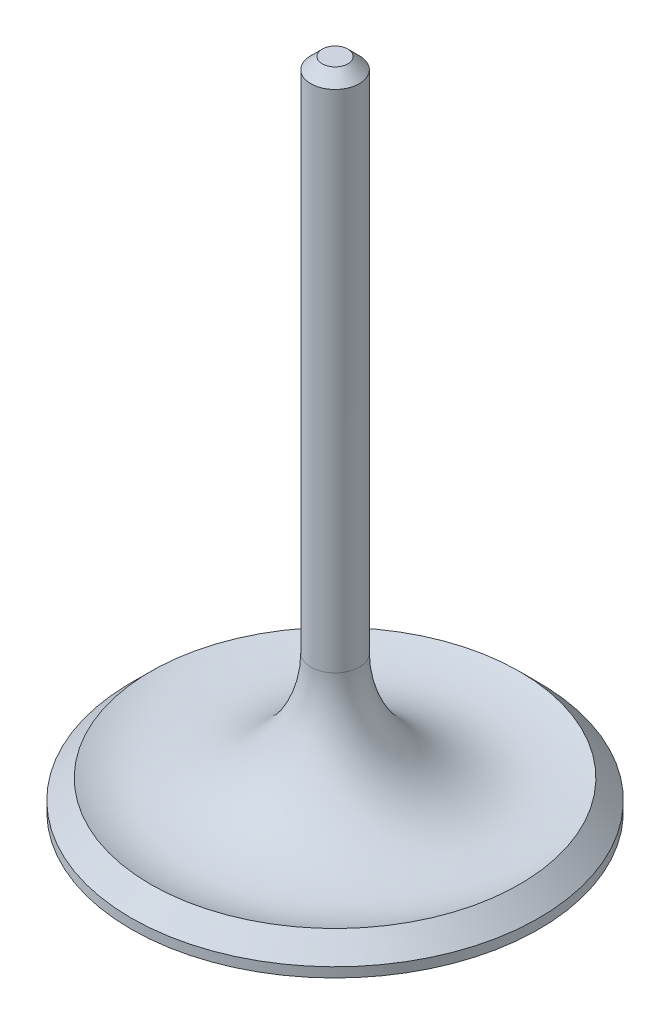
SolidWorks part; units mm, degrees
material "Ductile Iron"
ref_plane "Front Plane" through (0, 0, 0) normal (0, 0, 1) x (1, 0, 0)
ref_plane "Top Plane" through (0, 0, 0) normal (0, 1, 0) x (1, 0, 0)
ref_plane "Right Plane" through (0, 0, 0) normal (1, 0, 0) x (0, 0, -1)
sketch "Sketch2" plane through (0, 0, 0) normal (0, 0, 1) x (1, 0, 0)
  line L0 (0, 0) -> (26.67, 0)
  line L1 (26.67, 0) -> (26.67, 1.27)
  line L2 (26.67, 1.27) -> (24.13, 3.81)
  line L3 (3.175, 17.9527) -> (3.175, 85.55)
  line L4 (3.175, 85.55) -> (0, 85.55)
  line L5 (0, 85.55) -> (0, 0)
  arc A0 (24.13, 3.81) -> (3.175, 17.9527) centre (18.425, 17.9527) cw
  dimension "D5" = 15.25
  dimension "D1" = 85.55
  dimension "D2" = 26.67
  dimension "D3" = 1.27
  dimension "D4" = 3.81
  dimension "D6" = 45
  dimension "D7" = 3.175
revolve "Revolve1" add sketch "Sketch2" angle 360 about L5
chamfer "Chamfer1" distance 1.5 angle 45 1 edges at (0, 85.55, 3.175)
